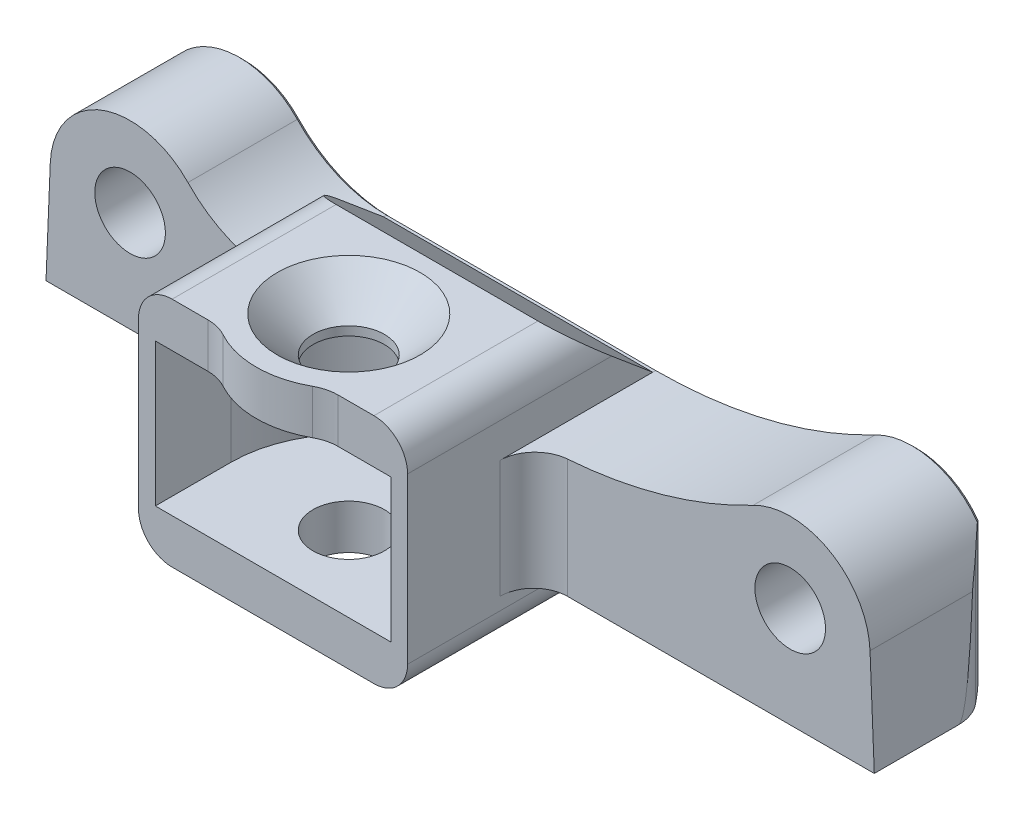
SolidWorks part; units mm, degrees
ref_plane "Front Plane" through (0, 0, 0) normal (0, 0, 1) x (1, 0, 0)
ref_plane "Top Plane" through (0, 0, 0) normal (0, 1, 0) x (1, 0, 0)
ref_plane "Right Plane" through (0, 0, 0) normal (1, 0, 0) x (0, 0, -1)
sketch "Sketch1" plane through (0, 0, 0) normal (1, 0, 0) x (0, 0, -1)
  line L0 (0, 0) -> (0, 14)
  line L1 (0, 14) -> (-0.8468, 14)
  line L2 (-0.8468, 14) -> (-10.5, 22.1)
  line L3 (-10.5, 22.1) -> (-30, 22.1)
  line L4 (-30, 22.1) -> (-30, -5.5)
  line L5 (-30, -5.5) -> (-11.5, -5.5)
  line L6 (-11.5, -5.5) -> (-4.9454, 0)
  line L7 (-4.9454, 0) -> (0, 0)
  line L8 (-30, -0.5) -> (-15.8736, -0.5) construction
  line L9 (-15.8736, -0.5) -> (-15.8736, 17.1) construction
  line L10 (-15.8736, 17.1) -> (-30, 17.1) construction
  dimension "D1" = 17.6
  dimension "D2" = 14
  dimension "D3" = 14.1264
  dimension "D4" = 5
  dimension "D5" = 19.5
  dimension "D6" = 30
  dimension "D7" = 40
  dimension "D8" = 40
  dimension "D9" = 5
  dimension "D10" = 0.5
  dimension "D11" = 18.5
extrude "Boss-Extrude1" add sketch "Sketch1" along normal mid plane 32
sketch "Sketch2" plane through (0, 22.1, 0) normal (0, 1, 0) x (1, 0, 0)
  line L0 (16, -30) -> (-16, -30) construction
  circle A0 centre (0, -21) radius 4.25
  dimension "D2" = 8.5
  dimension "D1" = 9
extrude "Cut-Extrude1" cut sketch "Sketch2" against normal through all
sketch "Sketch3" plane through (0, 22.1, 0) normal (0, 1, 0) x (1, 0, 0)
  line L0 (-14, -21) -> (-14, -59.0827)
  line L1 (-14, -59.0827) -> (14, -59.0827)
  line L2 (14, -59.0827) -> (14, -21)
  arc A0 (14, -21) -> (-14, -21) centre (0, -21) ccw
  dimension "D1" = 28
extrude "Cut-Extrude2" cut sketch "Sketch3" against normal blind 17 from offset 5.3 offset against normal yes
hole_wizard "CSK for M8 Flat Head Machine Screw1" positions "Sketch5" profile "Sketch4" countersink size "M8" standard "Ansi Metric" end condition through all
sketch "Sketch5" plane through (0, 22.1, 0) normal (0, 1, 0) x (-1, 0, 0)
  point P0 (0, 21)
sketch "Sketch4" plane through (0, 22.1, 21) normal (1, 0, 0) x (0, 0, 1)
  line L0 (0, 0) -> (0, 27.6)
  line L1 (0, 27.6) -> (4, 27.6)
  line L2 (4, 27.6) -> (4, 4.5)
  line L3 (4, 4.5) -> (8.5, 0)
  line L5 (8.5, 0) -> (0, 0)
  line L6 (-4, 4.5) -> (-8.5, 0) construction
  line L11 (0, -6.35) -> (0, 107.95) construction
  dimension "Thru Hole Dia." = 8
  dimension "Thru Hole Depth" = 27.6
  dimension "Near C'Sink Dia." = 17
  dimension "Near C'Sink Angle" = 90
sketch "Sketch6" plane through (0, 0, 0) normal (0, 0, -1) x (-1, 0, 0)
  line L0 (-16, 0) -> (16, 0) construction
  line L1 (-16, 14) -> (-16, 0)
  line L2 (-16, 0) -> (-56.5, 0)
  line L3 (-56.5, 0) -> (-55.992, 12.3892)
  line L4 (-16, 14) -> (16, 14) construction
  line L5 (42.992, 12.3892) -> (43.5, 0)
  line L6 (43.5, 0) -> (16, 0)
  line L7 (16, 0) -> (16, 14)
  line L8 (-16, 14) -> (16, 14) construction
  circle A0 centre (-46.5, 12) radius 4.2
  arc A1 (-42.0943, 20.4166) -> (-55.992, 12.3892) centre (-46.5, 12) ccw
  arc A2 (-16, 14) -> (-42.0943, 20.4166) centre (-16, 70.2667) cw
  circle A3 centre (33.5, 12) radius 4.2
  arc A4 (42.992, 12.3892) -> (26.6207, 18.5517) centre (33.5, 12) ccw
  arc A5 (16, 14) -> (26.6207, 18.5517) centre (16, 28.6667) ccw
  dimension "D3" = 19
  dimension "D4" = 8.4
  dimension "D1" = 12
  dimension "D2" = 46.5
  dimension "D5" = 10
  dimension "D6" = 100
  dimension "D7" = 80
extrude "Boss-Extrude2" add sketch "Sketch6" against normal blind 15
sketch "Sketch7" plane through (0, 0, 0) normal (0, 0, -1) x (-1, 0, 0)
  circle A0 centre (-46.5, 12) radius 4.2 construction
  circle A1 centre (-46.5, 12) radius 4.2
  circle A2 centre (33.5, 12) radius 4.2 construction
  circle A3 centre (33.5, 12) radius 4.2
extrude "Boss-Extrude3" add sketch "Sketch7" against normal blind 4
sketch "Sketch9" plane through (0, 0, 0) normal (0, -1, 0) x (1, 0, 0)
  line L0 (56.5, 0) -> (-43.5, 0) construction
  line L1 (56.5, 15) -> (56.5, 0) construction
  line L4 (-43.5, 15) -> (-43.5, 0) construction
  line L5 (-16, 15) -> (-43.5, 15) construction
  circle A0 centre (-38.5, 5) radius 2.6
  circle A1 centre (-25.5, 10) radius 2.6
  circle A2 centre (38.5, 10) radius 2.6
  circle A3 centre (51.5, 5) radius 2.6
  dimension "D1" = 5.2
  dimension "D2" = 18
  dimension "D3" = 18
  dimension "D4" = 5
  dimension "D5" = 5
  dimension "D6" = 5
  dimension "D7" = 5
extrude "Cut-Extrude3" cut sketch "Sketch9" against normal blind 6
sketch "Sketch11" plane through (0, 0, 15) normal (0, 0, 1) x (1, 0, 0)
  line L3 (-42.992, 12.3892) -> (-43.5, 0)
  line L4 (-43.5, 0) -> (-16, 0)
  line L5 (-16, 0) -> (-16, 14)
  line L6 (-42.992, 12.3892) -> (-43.5, 0)
  line L7 (-43.5, 0) -> (-16, 0)
  line L8 (-16, 0) -> (-16, 14)
  arc A2 (-26.6207, 18.5517) -> (-42.992, 12.3892) centre (-33.5, 12) ccw
  arc A3 (-26.6207, 18.5517) -> (-16, 14) centre (-16, 28.6667) ccw
  arc A4 (-26.6207, 18.5517) -> (-42.992, 12.3892) centre (-33.5, 12) ccw
  arc A5 (-26.6207, 18.5517) -> (-16, 14) centre (-16, 28.6667) ccw
  dimension "D1" = 0
extrude "Cut-Extrude4" cut sketch "Sketch11" against normal blind 1.5
fillet "Fillet2" radius 4 2 edges at (16, 7, 15) (-16, 7, 13.5)
fillet "Fillet3" radius 4 4 edges at (16, -5.5, 20.75) (-16, -5.5, 20.75) (-16, 22.1, 20.25) (16, 22.1, 20.25)
sketch "Sketch10" plane through (0, 22.1, 0) normal (0, 1, 0) x (1, 0, 0)
  line L0 (12, -30) -> (-12, -30) construction
  line L1 (6.3246, -30) -> (-6.3246, -30)
  arc A0 (-6.3246, -30) -> (6.3246, -30) centre (0, -21) ccw
  dimension "D1" = 22
extrude "Boss-Extrude4" add sketch "Sketch10" against normal up to surface (5.3 mm away) up to face at (0, 16.8, 25.25)
fillet "Fillet4" radius 5 2 edges at (6.3246, 19.45, 30) (-6.3246, 19.45, 30)
chamfer "Chamfer1" distance 0.6 angle 45 4 edges at (51.5, 0, 2.4) (38.5, 0, 7.4) (-25.5, 0, 7.4) (-38.5, 0, 2.4)
sketch "Sketch12" plane through (0, 0, 0) normal (0, -1, 0) x (1, 0, 0)
  line L0 (-42.3302, 1.7861) -> (-40.8315, 0)
  line L1 (56.5, 0) -> (-43.5, 0) construction
  line L2 (-40.8315, 0) -> (-43.5, 0)
  line L3 (-43.5, 0) -> (-43.5, 5)
  line L4 (-43.5, 13.5) -> (-43.5, 0) construction
  line L5 (55.3302, 1.7861) -> (53.8315, 0)
  line L6 (53.8315, 0) -> (56.5, 0)
  line L7 (56.5, 0) -> (56.5, 5)
  arc A0 (-43.5, 5) -> (-42.3302, 1.7861) centre (-38.5, 5) ccw
  arc A1 (55.3302, 1.7861) -> (56.5, 5) centre (51.5, 5) ccw
  dimension "D1" = 40
  dimension "D2" = 40
extrude "Cut-Extrude5" cut sketch "Sketch12" against normal through all
chamfer "Chamfer2" distance 0.5 angle 45 6 edges at (-33.8409, 21.4939, 0) (-21.7775, 15.1859, 0) (0, 14, 0) (29.4358, 15.6277, 0) (48.3843, 21.3113, 0) (6.5, 0, 0)
